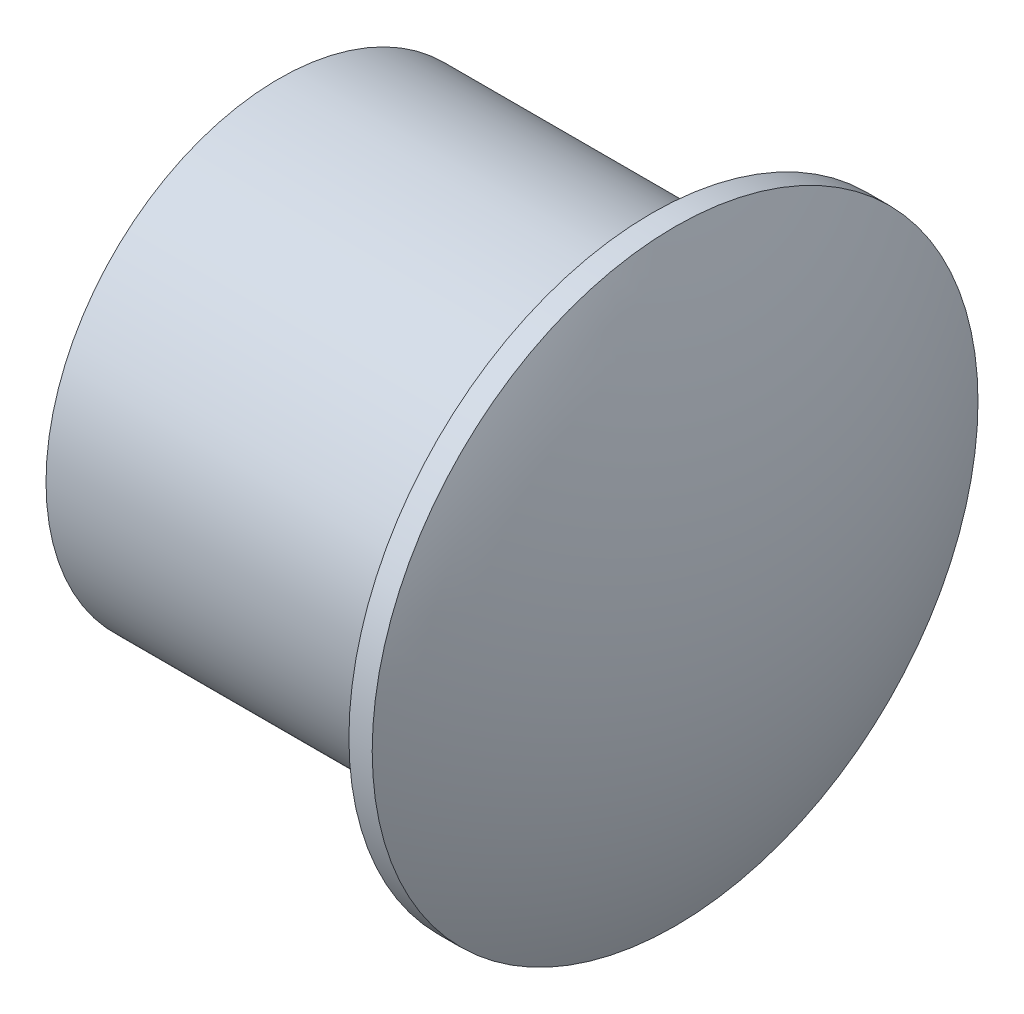
SolidWorks part; units mm, degrees
ref_plane "Front Plane" through (0, 0, 0) normal (0, 0, 1) x (1, 0, 0)
ref_plane "Top Plane" through (0, 0, 0) normal (0, 1, 0) x (1, 0, 0)
ref_plane "Right Plane" through (0, 0, 0) normal (1, 0, 0) x (0, 0, -1)
sketch "Sketch1" plane through (0, 0, 0) normal (0, 0, 1) x (1, 0, 0)
  line L0 (0, 0) -> (0, 10)
  line L1 (0, 10) -> (16, 10)
  line L2 (16, 10) -> (16, 13)
  line L3 (16, 13) -> (17, 13)
  line L5 (0, 0) -> (20, 0)
  arc A1 (20, 0) -> (17, 13) centre (-9.6667, 0) ccw
  dimension "D1" = 10
  dimension "D2" = 16
  dimension "D3" = 1
  dimension "D4" = 3
  dimension "D5" = 20
revolve "Revolve1" add sketch "Sketch1" angle 360 about L5
